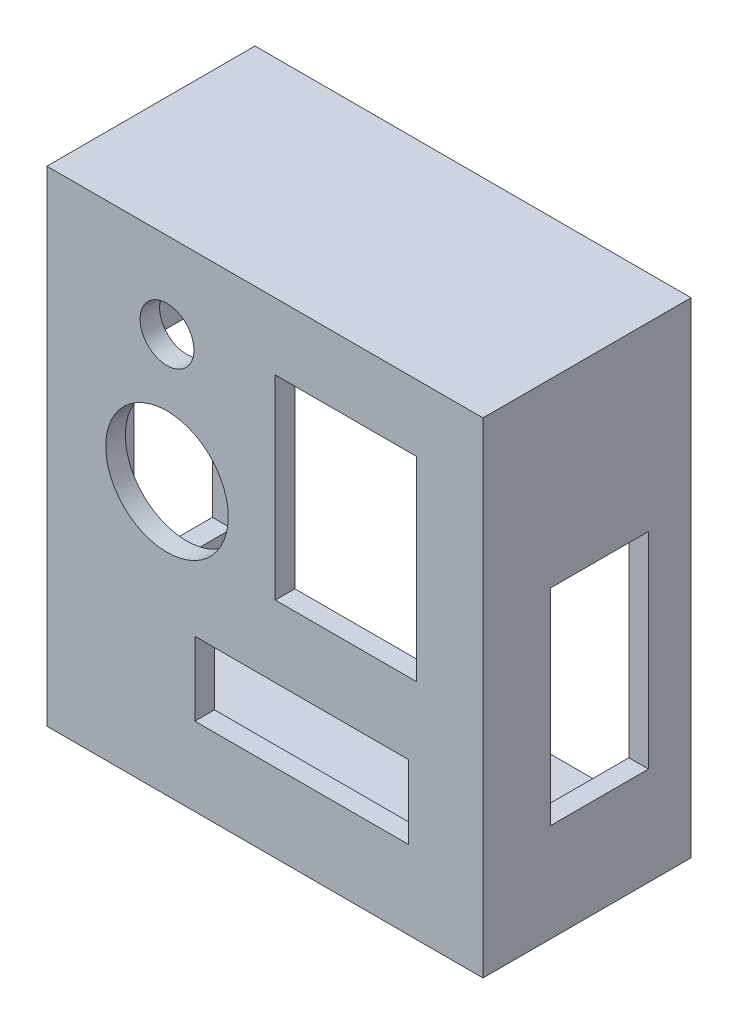
SolidWorks part; units mm, degrees
ref_plane "Front Plane" through (0, 0, 0) normal (0, 0, 1) x (1, 0, 0)
ref_plane "Top Plane" through (0, 0, 0) normal (0, 1, 0) x (1, 0, 0)
ref_plane "Right Plane" through (0, 0, 0) normal (1, 0, 0) x (0, 0, -1)
sketch "Sketch1" plane through (0, 0, 0) normal (0, 0, 1) x (1, 0, 0)
  line L1 (-64.2938, -72.2313) -> (64.2937, -72.2313)
  line L2 (-64.2938, -72.2313) -> (-64.2938, 72.2313)
  line L3 (-64.2938, 72.2313) -> (64.2937, 72.2313)
  line L4 (64.2937, -72.2313) -> (64.2937, 72.2313)
  line L5 (-64.2938, -72.2313) -> (64.2937, 72.2313) construction
  line L6 (-64.2938, 72.2313) -> (64.2937, -72.2313) construction
  point P0 (0, 0)
  dimension "D1" = 128.5875
  dimension "D2" = 144.4625
extrude "Boss-Extrude1" add sketch "Sketch1" against normal blind 61.0718 contours L3 L4 L1 L2
shell "Shell1" thickness 6.35
sketch "Sketch2" plane through (0, 0, 6.35) normal (0, 0, 1) x (1, 0, 0)
  line L0 (-70.6438, 78.5812) -> (70.6437, 78.5812) construction
  line L1 (-70.6438, -78.5812) -> (-70.6438, 78.5812) construction
  line L2 (70.6437, -78.5812) -> (70.6437, 78.5812) construction
  line L3 (3.3337, 56.9912) -> (49.0537, 56.9912)
  line L4 (3.3337, 56.9912) -> (3.3337, -6.1912)
  line L5 (3.3337, -6.1912) -> (49.0537, -6.1912)
  line L6 (49.0537, 56.9912) -> (49.0537, -6.1912)
  line L7 (3.3337, 56.9912) -> (49.0537, -6.1912) construction
  line L8 (3.3337, -6.1912) -> (49.0537, 56.9912) construction
  line L9 (-70.6438, -78.5812) -> (70.6437, -78.5812) construction
  line L10 (-22.7013, -29.3687) -> (46.5137, -29.3687)
  line L11 (-22.7013, -29.3687) -> (-22.7013, -53.1812)
  line L12 (-22.7013, -53.1812) -> (46.5137, -53.1812)
  line L13 (46.5137, -29.3687) -> (46.5137, -53.1812)
  line L14 (-22.7013, -29.3687) -> (46.5137, -53.1812) construction
  line L15 (-22.7013, -53.1812) -> (46.5137, -29.3687) construction
  circle A0 centre (-31.75, 50.8) radius 8.7312
  circle A1 centre (-31.75, 9.525) radius 19.8438
  point P8 (26.1937, 25.4)
  point P15 (11.9062, -41.275)
  dimension "D1" = 17.4625
  dimension "D4" = 39.6875
  dimension "D2" = 27.7812
  dimension "D3" = 38.8937
  dimension "D5" = 38.8937
  dimension "D6" = 69.0563
  dimension "D7" = 45.72
  dimension "D8" = 63.1825
  dimension "D9" = 21.59
  dimension "D10" = 21.59
  dimension "D11" = 69.215
  dimension "D12" = 23.8125
  dimension "D13" = 25.4
  dimension "D14" = 24.13
extrude "Cut-Extrude1" cut sketch "Sketch2" against normal through all
sketch "Sketch3" plane through (70.6437, 0, 0) normal (1, 0, 0) x (0, 0, -1)
  line L1 (15.5219, 19.9072) -> (47.2719, 19.9072)
  line L2 (15.5219, 19.9072) -> (15.5219, -46.7678)
  line L3 (15.5219, -46.7678) -> (47.2719, -46.7678)
  line L4 (47.2719, 19.9072) -> (47.2719, -46.7678)
  line L5 (15.5219, 19.9072) -> (47.2719, -46.7678) construction
  line L6 (15.5219, -46.7678) -> (47.2719, 19.9072) construction
  line L9 (61.0718, 78.5812) -> (-6.35, 78.5812) construction
  line L10 (-6.35, -78.5812) -> (-6.35, 78.5812) construction
  point P0 (31.3969, -13.4302)
  dimension "D1" = 31.75
  dimension "D2" = 66.675
  dimension "D3" = 58.674
  dimension "D4" = 21.8719
extrude "Cut-Extrude2" cut sketch "Sketch3" against normal through all
equation "\"diameter1\"= 0.6875in"
equation "\"topcircle1totop\" = 0.5 + 0.25 + ( 0.6875 / 2 )"
equation "\"leftcircle1toleft\"= 0.9375 + 0.25 + ( 0.6875 / 2 )"
equation "\"D1@Sketch2\"=\"diameter1\""
equation "\"D2@Sketch2\"=\"topcircle1totop\""
equation "\"D3@Sketch2\"=\"leftcircle1toleft\""
equation "\"diameter2\"= 1.5625in"
equation "\"topcircle2totop\"= 1.6875in + 0.25 + ( 1.5625 / 2 )"
equation "\"leftcircle2totop\" = 0.5in + 0.25 + ( 1.5625 / 2 )"
equation "\"D4@Sketch2\"=\"diameter2\""
equation "\"D5@Sketch2\"=\"leftcircle2totop\""
equation "\"D6@Sketch2\"=\"topcircle2totop\""
equation "\"boxedgetoside\"= 0.5in + 0.25 + 0.1"
equation "\"topboxtopedge\" = 1.8in"
equation "\"topboxsideedge\"= 2.4875in"
equation "\"bottomboxsideedge\"= 0.9375in"
equation "\"bottomboxtopedge\" = 2.725in"
equation "\"D7@Sketch2\"=\"topboxtopedge\""
equation "\"D8@Sketch2\"=\"topboxsideedge\""
equation "\"D9@Sketch2\"=\"boxedgetoside\""
equation "\"D10@Sketch2\"=\"boxedgetoside\""
equation "\"D11@Sketch2\"=\"bottomboxtopedge\""
equation "\"D12@Sketch2\"=\"bottomboxsideedge\""
equation "\"D13@Sketch2\"=\"bottomboxtobottomedge\""
equation "\"D14@Sketch2\"=\"bottomboxtorightedge\""
equation "\"sideboxtoleftedge\"= 0.5625 + 0.0772 / 2 + 0.26in"
equation "\"sideboxtotopedge\" = 2 + 0.25 + 0.06in"
equation "\"sideboxwidth\"= 1.25in"
equation "\"sideboxheight\"= 2.625in"
equation "\"D1@Sketch3\"=\"sideboxwidth\""
equation "\"D2@Sketch3\"=\"sideboxheight\""
equation "\"D3@Sketch3\"=\"sideboxtotopedge\""
equation "\"D4@Sketch3\"=\"sideboxtoleftedge\""
equation "\"bottomboxtorightedge\"= 0.75 + 0.2in"
equation "\"bottomboxtobottomedge\"= 0.75 + 0.25in"
